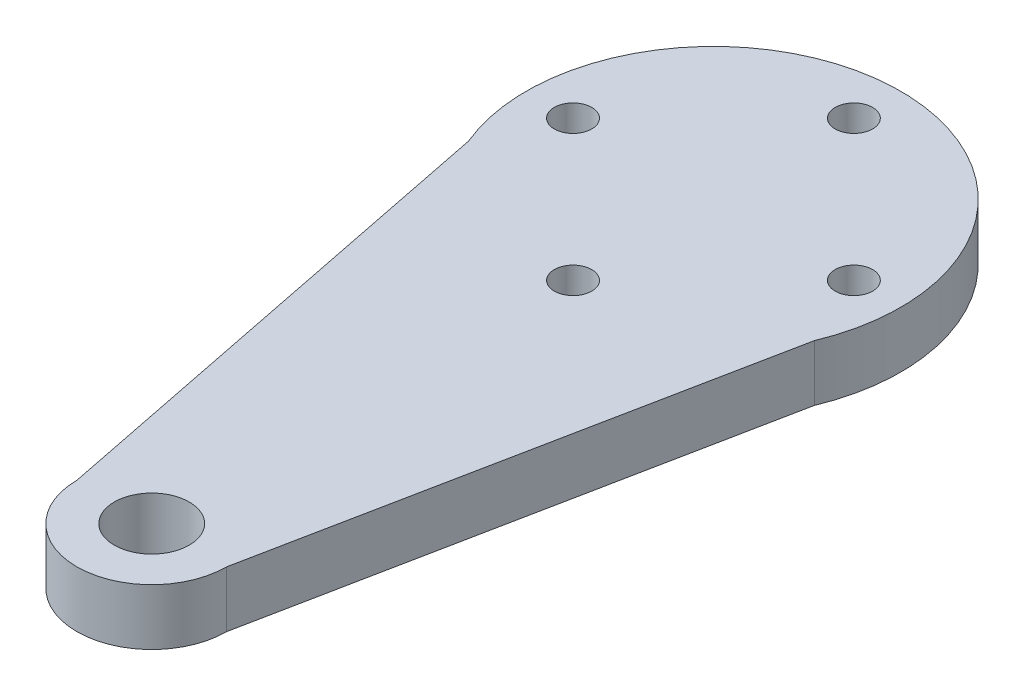
SolidWorks part; units mm, degrees
material "Acrílico (Impacto medio-alto)"
ref_plane "Alzado" through (0, 0, 0) normal (0, 0, 1) x (1, 0, 0)
ref_plane "Planta" through (0, 0, 0) normal (0, 1, 0) x (1, 0, 0)
ref_plane "Vista lateral" through (0, 0, 0) normal (1, 0, 0) x (0, 0, -1)
sketch "Croquis1" plane through (0, 0, 0) normal (0, 1, 0) x (1, 0, 0)
  line L0 (0, 0) -> (7.5, 0) construction
  line L1 (0, 0) -> (-7.5, 0) construction
  line L2 (0, 0) -> (0, 7.5) construction
  line L3 (0, 0) -> (0, -7.5) construction
  line L4 (0, 0) -> (0, -30) construction
  line L5 (-4, -30) -> (-9.2308, -3.8462)
  line L6 (4, -30) -> (9.2308, -3.8462)
  circle A0 centre (0, 7.5) radius 1
  circle A1 centre (7.5, 0) radius 1
  circle A2 centre (0, -7.5) radius 1
  circle A3 centre (-7.5, 0) radius 1
  arc A4 (9.2308, -3.8462) -> (-9.2308, -3.8462) centre (0, 0) ccw
  circle A5 centre (0, -30) radius 2
  arc A6 (-4, -30) -> (4, -30) centre (0, -30) ccw
extrude "Saliente-Extruir1" add sketch "Croquis1" along normal blind 3
